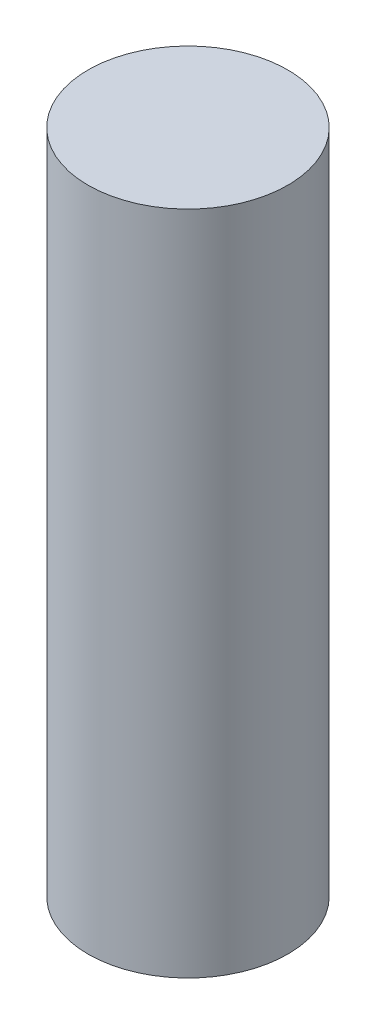
SolidWorks part; units mm, degrees
ref_plane "Front Plane" through (0, 0, 0) normal (0, 0, 1) x (1, 0, 0)
ref_plane "Top Plane" through (0, 0, 0) normal (0, 1, 0) x (1, 0, 0)
ref_plane "Right Plane" through (0, 0, 0) normal (1, 0, 0) x (0, 0, -1)
sketch "Sketch1" plane through (0, 0, 0) normal (0, 1, 0) x (1, 0, 0)
  circle A1 centre (22.352, 0) radius 3.048
  dimension "D2" = 6.096
extrude "Boss-Extrude1" add sketch "Sketch1" along normal blind 20.32
